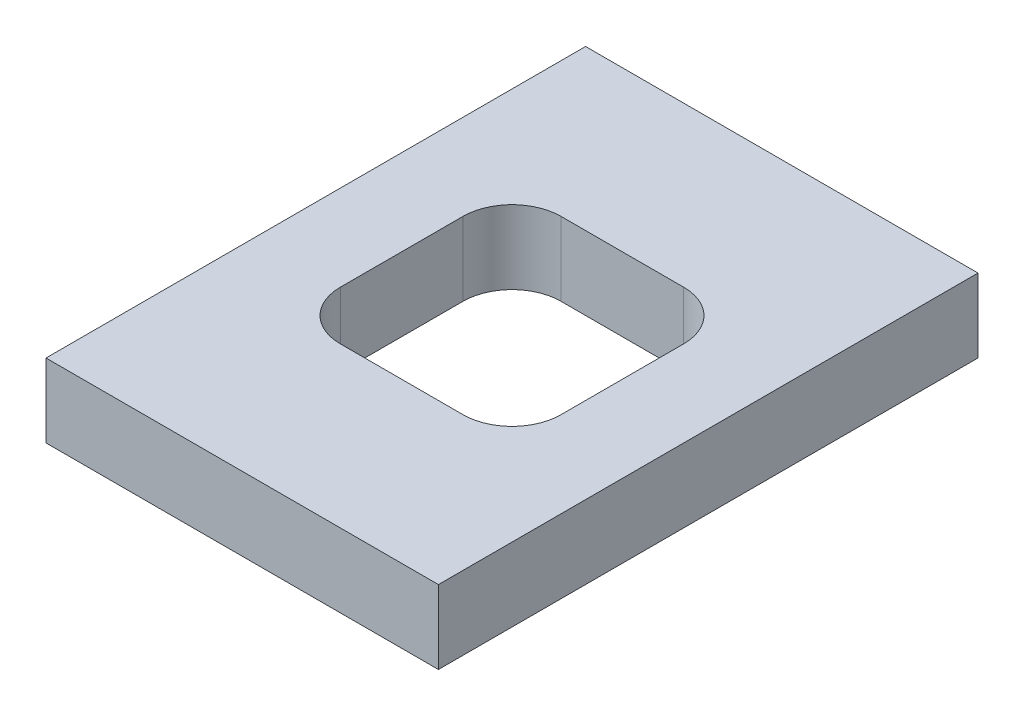
SolidWorks part; units mm, degrees
ref_plane "Plano frontal" through (0, 0, 0) normal (0, 0, 1) x (1, 0, 0)
ref_plane "Plano superior" through (0, 0, 0) normal (0, 1, 0) x (1, 0, 0)
ref_plane "Plano direito" through (0, 0, 0) normal (1, 0, 0) x (0, 0, -1)
sketch "Sketch1" plane through (0, 0, 0) normal (0, 1, 0) x (1, 0, 0)
  line L1 (-4.5, 4.5) -> (4.5, 4.5)
  line L2 (-4.5, 4.5) -> (-4.5, -4.5)
  line L3 (-4.5, -4.5) -> (4.5, -4.5)
  line L4 (4.5, 4.5) -> (4.5, -4.5)
  line L5 (-8, 11) -> (8, 11)
  line L6 (-8, 11) -> (-8, -11)
  line L7 (-8, -11) -> (8, -11)
  line L8 (8, 11) -> (8, -11)
  point P9 (-4.5, 0)
  point P11 (0, 4.5)
  point P12 (0, 11)
  dimension "D1" = 9
  dimension "D2" = 9
  dimension "D3" = 6.5
  dimension "D4" = 3.5
  dimension "D5" = 22
extrude "Boss-Extrude1" add sketch "Sketch1" along normal mid plane 3
fillet "Fillet1" radius 2 4 edges at (-4.5, 0, -4.5) (4.5, 0, -4.5) (4.5, 0, 4.5) (-4.5, 0, 4.5)
